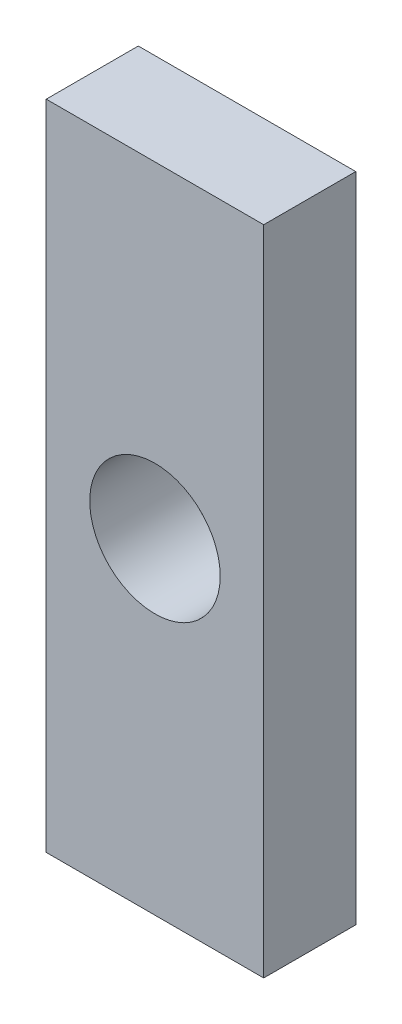
SolidWorks part; units mm, degrees
ref_plane "Front Plane" through (0, 0, 0) normal (0, 0, 1) x (1, 0, 0)
ref_plane "Top Plane" through (0, 0, 0) normal (0, 1, 0) x (1, 0, 0)
ref_plane "Right Plane" through (0, 0, 0) normal (1, 0, 0) x (0, 0, -1)
sketch "Sketch1" plane through (0, 0, 0) normal (0, 0, 1) x (1, 0, 0)
  line L0 (0, 22.5) -> (15, 22.5) construction
  line L1 (0, 0) -> (15, 0)
  line L2 (0, 0) -> (0, 45)
  line L3 (0, 45) -> (15, 45)
  line L4 (15, 0) -> (15, 45)
  line L5 (7.5, 45) -> (7.5, 0) construction
  dimension "D1" = 15
  dimension "D2" = 45
extrude "Boss-Extrude1" add sketch "Sketch1" along normal blind 6.35
sketch "Sketch3" plane through (0, 0, 6.35) normal (0, 0, 1) x (1, 0, 0)
  line L0 (0, 45) -> (15, 0) construction
  line L1 (0, 0) -> (50, 45) construction
  line L2 (15, 45) -> (0, 45) construction
  circle A0 centre (7.5, 22.5) radius 4.5
extrude "Cut-Extrude1" cut sketch "Sketch3" against normal through all
